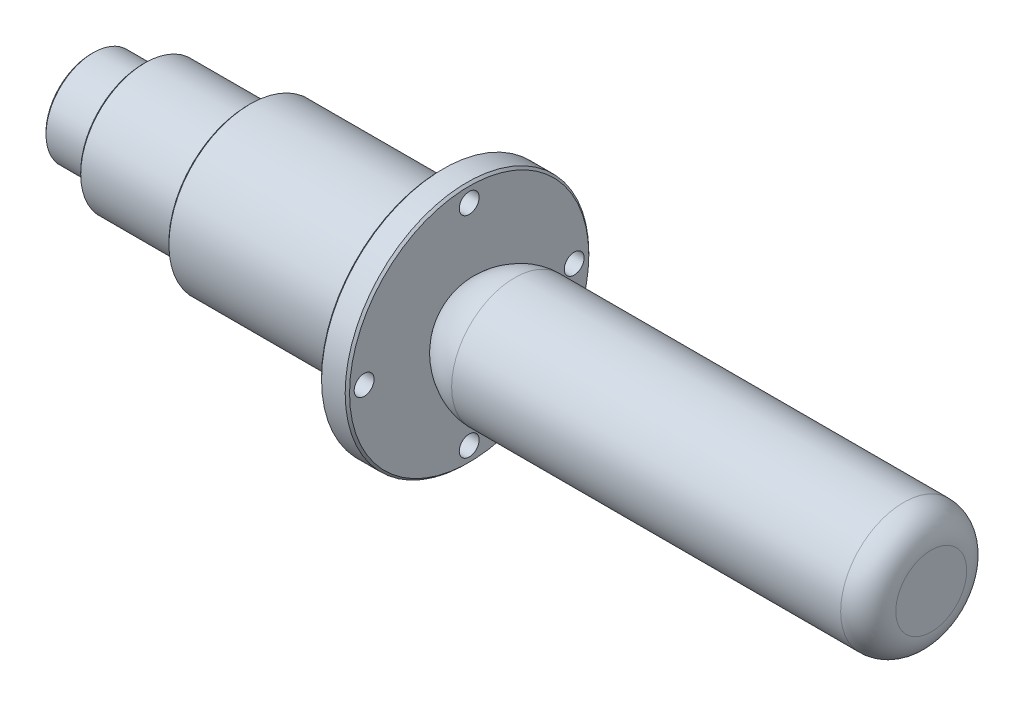
SolidWorks part; units mm, degrees
ref_plane "Front Plane" through (0, 0, 0) normal (0, 0, 1) x (1, 0, 0)
ref_plane "Top Plane" through (0, 0, 0) normal (0, 1, 0) x (1, 0, 0)
ref_plane "Right Plane" through (0, 0, 0) normal (1, 0, 0) x (0, 0, -1)
sketch "Sketch1" plane through (0, 0, 0) normal (0, 0, 1) x (1, 0, 0)
  line L0 (-19.6703, 0) -> (-19.6703, 8.5806)
  line L1 (-19.6703, 8.5806) -> (-10.2723, 8.5806)
  line L2 (-10.2723, 8.5806) -> (-10.2723, 11.684)
  line L3 (-10.2723, 11.684) -> (8.7777, 11.684)
  line L4 (8.7777, 11.684) -> (8.7777, 14.732)
  line L5 (8.7777, 14.732) -> (43.8297, 14.732)
  line L6 (43.8297, 14.732) -> (43.8297, 22.098)
  line L7 (43.8297, 22.098) -> (48.9097, 22.098)
  line L8 (48.9097, 22.098) -> (48.9097, 7.0552)
  line L9 (57.156, 11.43) -> (127.7297, 11.43)
  line L10 (-19.6703, 0) -> (132.7297, 0)
  line L11 (132.7297, 0) -> (132.7297, 6.43)
  arc A0 (127.7297, 11.43) -> (132.7297, 6.43) centre (127.7297, 6.43) cw
  spline S0 degree 3 poles (48.9097, 7.0552) (50.7457, 9.4694) (54.0783, 11.43) (57.156, 11.43) knots 0 0 0 0 1 1 1 1
  point P17 (92.4428, 11.43)
  dimension "D1" = 5
  dimension "D2" = 11.43
  dimension "D3" = 11.684
  dimension "D4" = 14.732
  dimension "D5" = 22.098
  dimension "D6" = 5.08
  dimension "D7" = 35.052
  dimension "D8" = 68.58
  dimension "D9" = 152.4
  dimension "D10" = 19.05
revolve "Revolve1" add sketch "Sketch1" angle 360 about L10
sketch "Sketch2" plane through (48.9097, 0, 0) normal (1, 0, 0) x (0, 0, -1)
  circle A0 centre (0, 0) radius 19.05 construction
  circle A1 centre (0, 19.05) radius 1.8034
  dimension "D1" = 38.1
extrude "Cut-Extrude1" cut sketch "Sketch2" against normal up to next (5.08 mm away)
pattern_circular "CirPattern2" count 4 over 360 about axis through (0, 0, 0) along (1, 0, 0) of "Cut-Extrude1"
chamfer "Chamfer1" distance 0.3969 angle 45 5 edges at (48.9097, 0, 22.098) (43.8297, 0, 22.098) (8.7777, 0, 14.732) (-10.2723, 0, 11.684) (-19.6703, 0, 8.5806)
equation "\"D3@Sketch1\"=0.92/2"
equation "\"D4@Sketch1\"=1.16/2"
